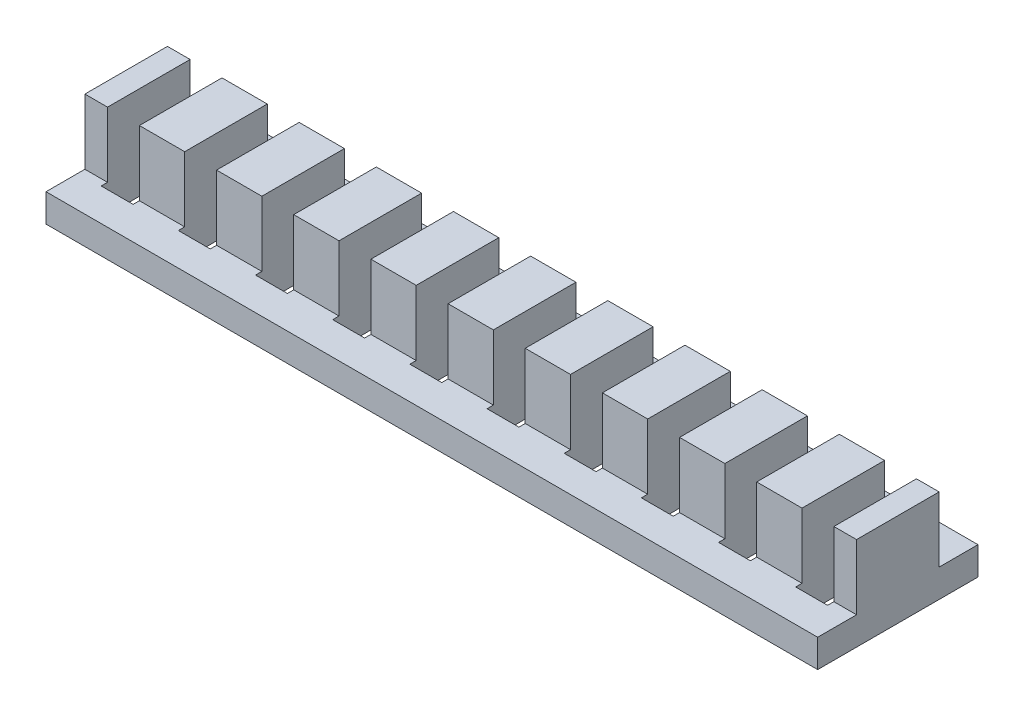
SolidWorks part; units mm, degrees
ref_plane "Front Plane" through (0, 0, 0) normal (0, 0, 1) x (1, 0, 0)
ref_plane "Top Plane" through (0, 0, 0) normal (0, 1, 0) x (1, 0, 0)
ref_plane "Right Plane" through (0, 0, 0) normal (1, 0, 0) x (0, 0, -1)
sketch "Sketch1" plane through (0, 0, 0) normal (0, 1, 0) x (1, 0, 0)
  line L1 (-38.5, -8) -> (38.5, -8)
  line L2 (-38.5, -8) -> (-38.5, 8)
  line L3 (-38.5, 8) -> (38.5, 8)
  line L4 (38.5, -8) -> (38.5, 8)
  line L5 (-38.5, -8) -> (38.5, 8) construction
  line L6 (-38.5, 8) -> (38.5, -8) construction
  point P0 (0, 0)
  dimension "D1" = 16
  dimension "D2" = 77
extrude "Boss-Extrude1" add sketch "Sketch1" along normal blind 2.8
sketch "Sketch2" plane through (0, 2.8, 0) normal (0, 1, 0) x (1, 0, 0)
  line L0 (-38.5, 8) -> (-38.5, -8) construction
  line L1 (-38.5, 4.12) -> (38.5, 4.12)
  line L2 (-38.5, 4.12) -> (-38.5, -4.12)
  line L3 (-38.5, -4.12) -> (38.5, -4.12)
  line L4 (38.5, 4.12) -> (38.5, -4.12)
  line L5 (38.5, -8) -> (38.5, 8) construction
  point P8 (-38.5, 0)
  point P9 (-38.5, 0)
  dimension "D1" = 8.24
extrude "Boss-Extrude2" add sketch "Sketch2" along normal blind 6.5
sketch "Sketch4" plane through (0, 0, 0) normal (0, -1, 0) x (1, 0, 0)
  line L0 (-28.54, 4.75) -> (-28.54, -4.75)
  line L1 (-36.24, 4.75) -> (-33.06, 4.75)
  line L2 (-36.24, 4.75) -> (-36.24, -4.75)
  line L3 (-36.24, -4.75) -> (-33.06, -4.75)
  line L4 (-33.06, 4.75) -> (-33.06, -4.75)
  line L5 (-28.54, 4.75) -> (-25.36, 4.75)
  line L6 (-34.65, 4.75) -> (-34.65, 8) construction
  line L7 (-38.5, 8) -> (38.5, 8) construction
  line L8 (-34.65, -4.75) -> (-34.65, -8) construction
  line L9 (38.5, -8) -> (-38.5, -8) construction
  line L10 (-25.36, 4.75) -> (-25.36, -4.75)
  line L11 (-28.54, -4.75) -> (-25.36, -4.75)
  line L12 (-20.84, 4.75) -> (-20.84, -4.75)
  line L13 (-20.84, 4.75) -> (-17.66, 4.75)
  line L14 (-17.66, 4.75) -> (-17.66, -4.75)
  line L15 (-20.84, -4.75) -> (-17.66, -4.75)
  line L16 (-13.14, 4.75) -> (-13.14, -4.75)
  line L17 (-13.14, 4.75) -> (-9.96, 4.75)
  line L18 (-9.96, 4.75) -> (-9.96, -4.75)
  line L19 (-13.14, -4.75) -> (-9.96, -4.75)
  line L20 (-5.44, 4.75) -> (-5.44, -4.75)
  line L21 (-5.44, 4.75) -> (-2.26, 4.75)
  line L22 (-2.26, 4.75) -> (-2.26, -4.75)
  line L23 (-5.44, -4.75) -> (-2.26, -4.75)
  line L24 (2.26, 4.75) -> (2.26, -4.75)
  line L25 (2.26, 4.75) -> (5.44, 4.75)
  line L26 (5.44, 4.75) -> (5.44, -4.75)
  line L27 (2.26, -4.75) -> (5.44, -4.75)
  line L28 (9.96, 4.75) -> (9.96, -4.75)
  line L29 (9.96, 4.75) -> (13.14, 4.75)
  line L30 (13.14, 4.75) -> (13.14, -4.75)
  line L31 (9.96, -4.75) -> (13.14, -4.75)
  line L32 (17.66, 4.75) -> (17.66, -4.75)
  line L33 (17.66, 4.75) -> (20.84, 4.75)
  line L34 (20.84, 4.75) -> (20.84, -4.75)
  line L35 (17.66, -4.75) -> (20.84, -4.75)
  line L36 (25.36, 4.75) -> (25.36, -4.75)
  line L37 (25.36, 4.75) -> (28.54, 4.75)
  line L38 (28.54, 4.75) -> (28.54, -4.75)
  line L39 (25.36, -4.75) -> (28.54, -4.75)
  line L40 (33.06, 4.75) -> (33.06, -4.75)
  line L41 (33.06, 4.75) -> (36.24, 4.75)
  line L42 (36.24, 4.75) -> (36.24, -4.75)
  line L43 (33.06, -4.75) -> (36.24, -4.75)
  line L44 (-2.26, 0) -> (2.26, 0) construction
  line L45 (-26.95, 4.75) -> (-26.95, 8) construction
  point P50 (0, 0)
  dimension "D1" = 3.18
  dimension "D2" = 9.5
  dimension "D3" = 10
  dimension "D5" = 7.7
extrude "Cut-Extrude1" cut sketch "Sketch4" against normal through all
equation "\"Width\"= 16"
equation "\"D1@Sketch1\"=\"Width\""
equation "\"D2@Sketch1\"=\"Length\""
equation "\"pinWidth\" = 8.24"
equation "\"D1@Sketch2\"=\"pinWidth\""
equation "\"pinCount\"= 10"
equation "\"interspace\"= 4.52"
equation "\"pinLength\"= 3.18"
equation "\"Length\"= ( \"pinLength\" + \"interspace\" ) * \"pinCount\""
equation "\"mLength\" = \"Width\""
